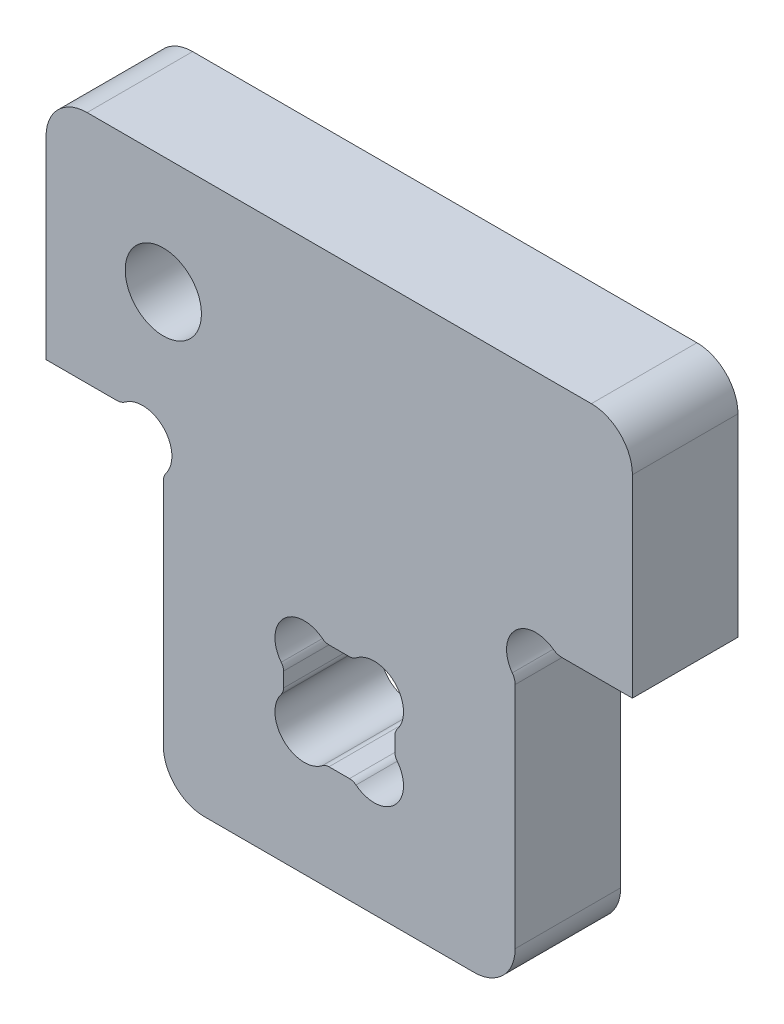
SolidWorks part; units mm, degrees
ref_plane "Plan de face" through (0, 0, 0) normal (0, 0, 1) x (1, 0, 0)
ref_plane "Plan de dessus" through (0, 0, 0) normal (0, 1, 0) x (1, 0, 0)
ref_plane "Plan de droite" through (0, 0, 0) normal (1, 0, 0) x (0, 0, -1)
sketch "Esquisse2" plane through (0, 0, 0) normal (0, 0, 1) x (1, 0, 0)
  line L0 (0, 54) -> (-3.6998, 50.3002) construction
  line L1 (0, 0) -> (60, 0)
  line L2 (0, 0) -> (0, 46.0122)
  line L3 (30, 0) -> (30, 94) construction
  line L4 (60, 0) -> (60, 46.0122)
  line L5 (67.9878, 54) -> (80, 54)
  line L6 (80, 94) -> (80, 54)
  line L7 (-7.9878, 54) -> (-20, 54)
  line L8 (-20, 94) -> (-20, 54)
  line L9 (-20, 94) -> (80, 94)
  arc A0 (0.4882, 47.4963) -> (-6.5037, 54.4882) centre (-3.5355, 50.4645) ccw
  arc A1 (0, 46.0122) -> (0.4882, 47.4963) centre (2.5, 46.0122) cw
  arc A2 (-6.5037, 54.4882) -> (-7.9878, 54) centre (-7.9878, 56.5) cw
  arc A3 (60, 46.0122) -> (59.5118, 47.4963) centre (57.5, 46.0122) ccw
  arc A4 (59.5118, 47.4963) -> (66.5037, 54.4882) centre (63.5355, 50.4645) cw
  arc A5 (66.5037, 54.4882) -> (67.9878, 54) centre (67.9878, 56.5) ccw
  dimension "D3" = 45
  dimension "D4" = 5
  dimension "D7" = 2.5
  dimension "D1" = 30
  dimension "D6" = 50
  dimension "D2" = 40
  dimension "D5" = 54
extrude "Boss.-Extru.2" add sketch "Esquisse2" along normal blind 18
sketch "Esquisse1" plane through (0, 0, 0) normal (0, 0, 1) x (1, 0, 0)
  line L0 (30, 0) -> (30, 18) construction
  line L1 (0, 0) -> (60, 0) construction
  line L3 (39.5, 28.2488) -> (39.5, 25.7512)
  line L4 (28.2512, 36) -> (31.7488, 36)
  line L5 (20.5, 27) -> (39.5, 27) construction
  line L6 (20.5, 28.2488) -> (20.5, 25.7512)
  line L7 (28.2512, 18) -> (31.7488, 18)
  line L8 (-20, 54) -> (-7.9878, 54) construction
  line L9 (20.5, 18) -> (30, 27.5) construction
  arc A0 (20.1123, 24.6353) -> (27.1353, 17.6123) centre (24.0355, 21.5355) ccw
  arc A1 (20.1123, 24.6353) -> (20.5, 25.7512) centre (18.7, 25.7512) ccw
  arc A2 (27.1353, 17.6123) -> (28.2512, 18) centre (28.2512, 16.2) cw
  arc A3 (32.8647, 17.6123) -> (31.7488, 18) centre (31.7488, 16.2) ccw
  arc A4 (39.8877, 24.6353) -> (32.8647, 17.6123) centre (35.9645, 21.5355) cw
  arc A5 (39.8877, 24.6353) -> (39.5, 25.7512) centre (41.3, 25.7512) cw
  arc A6 (39.8877, 29.3647) -> (39.5, 28.2488) centre (41.3, 28.2488) ccw
  arc A7 (39.8877, 29.3647) -> (32.8647, 36.3877) centre (35.9645, 32.4645) ccw
  arc A8 (32.8647, 36.3877) -> (31.7488, 36) centre (31.7488, 37.8) cw
  arc A9 (27.1353, 36.3877) -> (28.2512, 36) centre (28.2512, 37.8) ccw
  arc A10 (20.1123, 29.3647) -> (27.1353, 36.3877) centre (24.0355, 32.4645) cw
  arc A11 (20.1123, 29.3647) -> (20.5, 28.2488) centre (18.7, 28.2488) cw
  point P2 (30, 0)
  point P21 (30, 18)
  dimension "D7" = 5
  dimension "D1" = 1.8
  dimension "D3" = 45
  dimension "D5" = 9
  dimension "D6" = 9.5
  dimension "D2" = 18
extrude "Enlèv. mat.-Extru.1" cut sketch "Esquisse1" along normal through all
fillet "Congé1" radius 7 4 edges at (0, 0, 9) (-20, 94, 9) (80, 94, 9) (60, 0, 9)
sketch "Esquisse3" plane through (0, 0, 18) normal (0, 0, 1) x (1, 0, 0)
  line L0 (73, 94) -> (-13, 94) construction
  line L1 (-20, 87) -> (-20, 54) construction
  circle A0 centre (0, 74) radius 6.5
  dimension "D1" = 13
  dimension "D2" = 20
  dimension "D3" = 20
extrude "Enlèv. mat.-Extru.2" cut sketch "Esquisse3" against normal through all
equation "\"D1@Boss.-Extru.2\" = \"material_thickness\""
equation "\"D7@Esquisse1\" = \"tool_diameter\" / 2 + \"hole_clearance\""
equation "\"D6@Esquisse1\" = \"material_thickness\" / 2 + \"clearance\""
equation "\"D5@Esquisse1\" = \"material_thickness\" / 2"
equation "\"D4@Esquisse2\"= \"tool_diameter\" / 2 + \"hole_clearance\""
equation "\"D1@Congé1\"=\"fillet\""
equation "\"D1@Esquisse1\"=\"material_thickness\"/10"
equation "\"D5@Esquisse2\" = \"material_thickness\" * 3"
equation "\"tool_diameter\"=9"
equation "\"hole_clearance\"=0.5"
equation "\"material_thickness\"=18"
equation "\"clearance\"=0.5"
equation "\"outer_slot\"=0.5"
equation "\"fillet\"=7"
equation "\"D7@Esquisse2\"=\"D4@Esquisse2\"/2"
equation "\"D2@Esquisse1\"=\"material_thickness\""
equation "\"string\"= 2 * \"tool_diameter\" / 2 * cos ( 45deg )"
equation "\"angle\"= IIF ( \"string\" < \"limit\" , 45 , ( 180 - 2 * arcsin ( \"ThicknessVStool_dia\" ) ) / 2 )"
equation "\"limit\"= \"material_thickness\" / 2 * 9 / 10"
equation "\"ThicknessVStool_dia\"= IIF ( \"limit\" / \"tool_diameter\" > 1 , 1 , \"limit\" / \"tool_diameter\" )"
equation "\"D3@Esquisse1\"=\"angle\""
